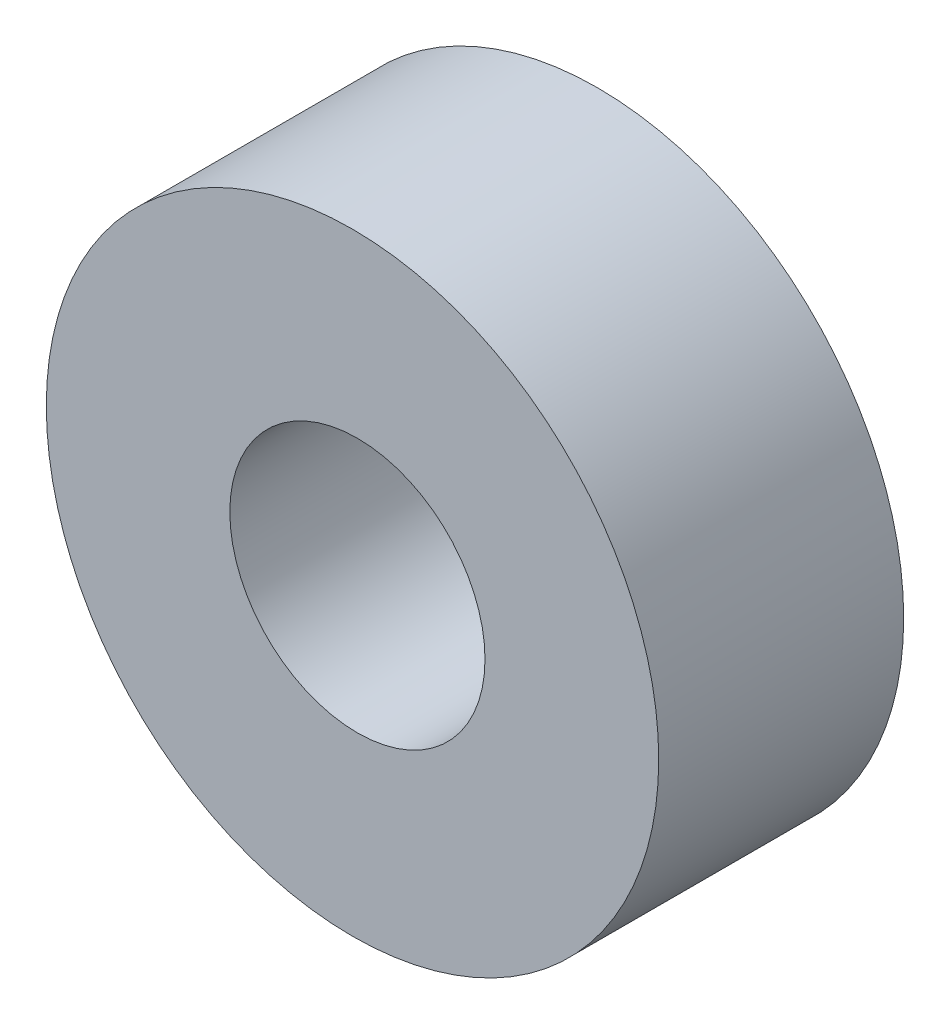
SolidWorks part; units mm, degrees
ref_plane "Front Plane" through (0, 0, 0) normal (0, 0, 1) x (1, 0, 0)
ref_plane "Top Plane" through (0, 0, 0) normal (0, 1, 0) x (1, 0, 0)
ref_plane "Right Plane" through (0, 0, 0) normal (1, 0, 0) x (0, 0, -1)
sketch "Sketch1" plane through (0, 0, 0) normal (0, 0, 1) x (1, 0, 0)
  circle A0 centre (0, 0) radius 12.5
  circle A1 centre (-0.48, 0) radius 30
  dimension "D1" = 60
  dimension "D2" = 25
extrude "Boss-Extrude1" add sketch "Sketch1" along normal blind 24
